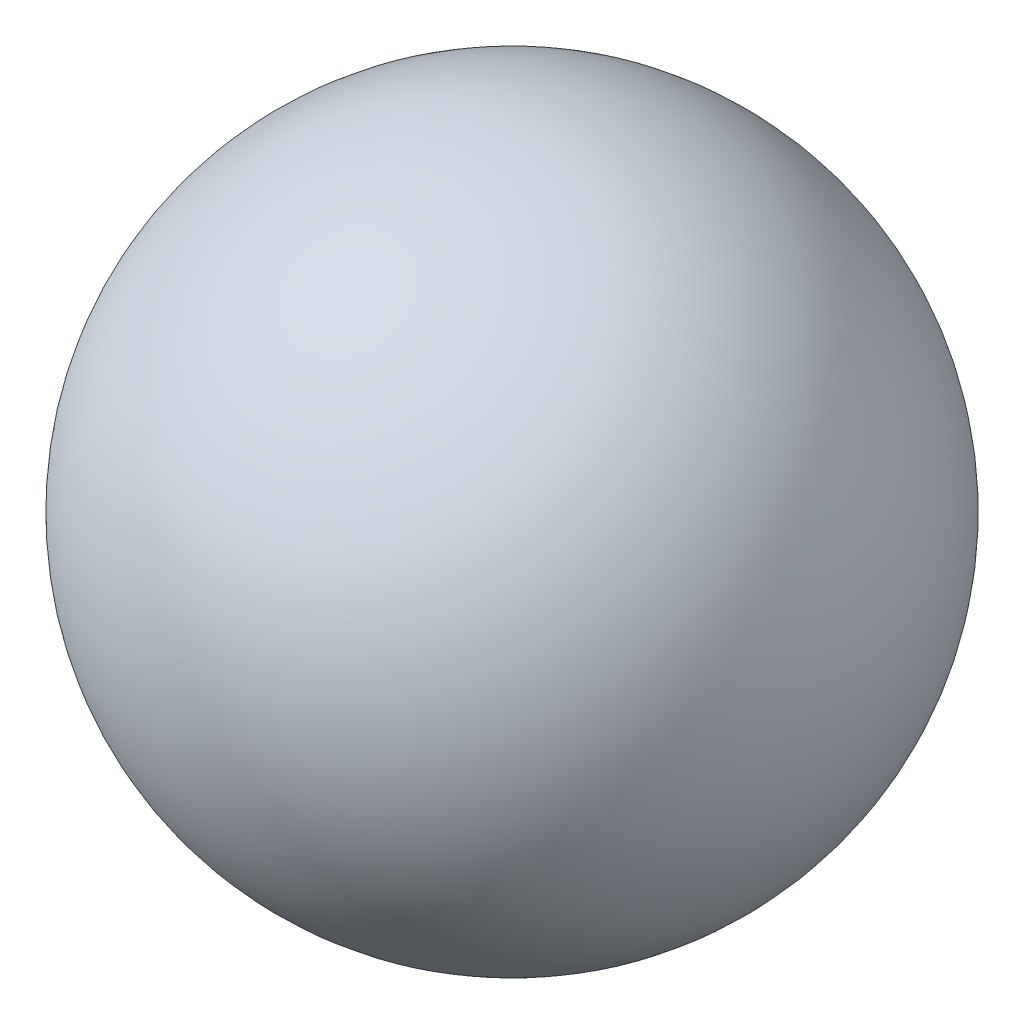
SolidWorks part; units mm, degrees
ref_plane "Front Plane" through (0, 0, 0) normal (0, 0, 1) x (1, 0, 0)
ref_plane "Top Plane" through (0, 0, 0) normal (0, 1, 0) x (1, 0, 0)
ref_plane "Right Plane" through (0, 0, 0) normal (1, 0, 0) x (0, 0, -1)
sketch "Sketch1" plane through (0, 0, 0) normal (0, 0, 1) x (1, 0, 0)
  line L0 (0, 127) -> (0, -127)
  arc A0 (0, -127) -> (0, 127) centre (0, 0) ccw
  dimension "D1" = 254
revolve "Revolve1" add sketch "Sketch1" angle 360 about L0
